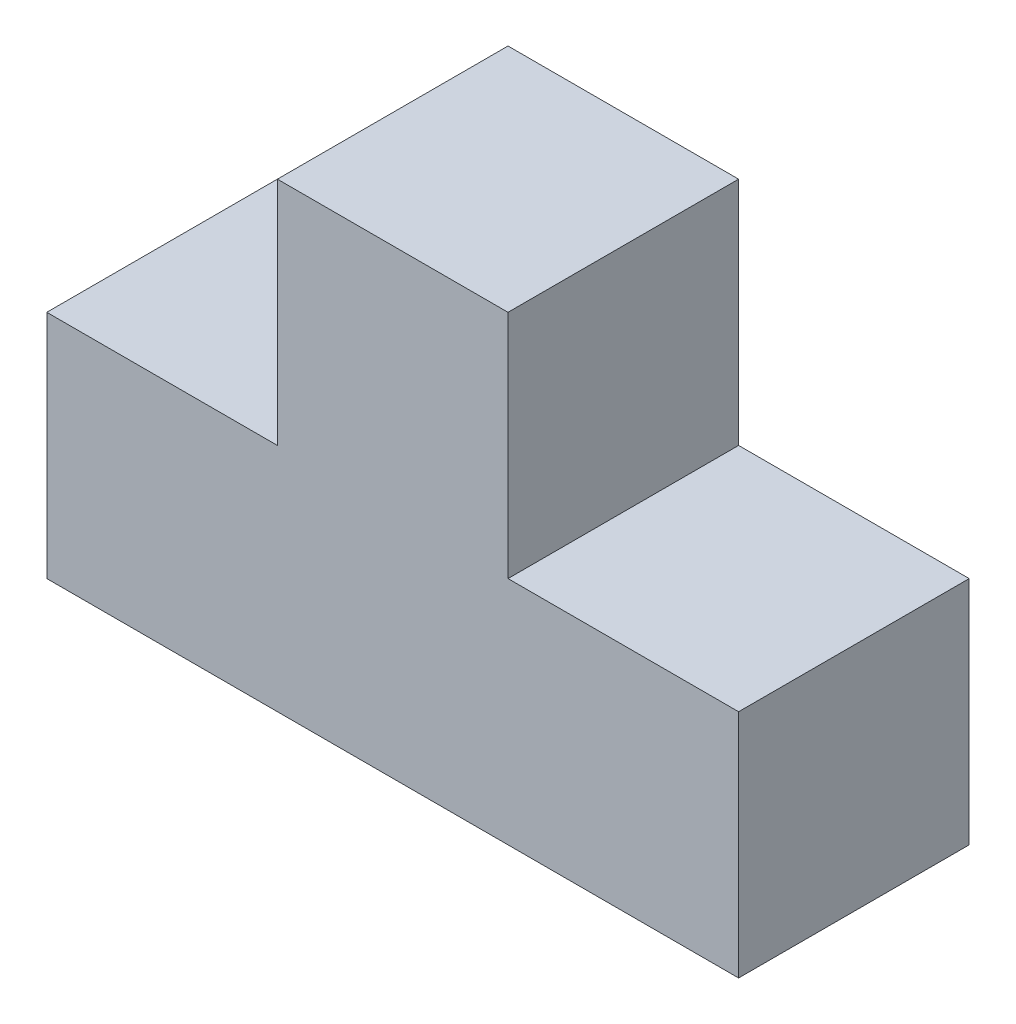
SolidWorks part; units mm, degrees
ref_plane "Front Plane" through (0, 0, 0) normal (0, 0, 1) x (1, 0, 0)
ref_plane "Top Plane" through (0, 0, 0) normal (0, 1, 0) x (1, 0, 0)
ref_plane "Right Plane" through (0, 0, 0) normal (1, 0, 0) x (0, 0, -1)
sketch "Sketch1" plane through (0, 0, 0) normal (0, 0, 1) x (1, 0, 0)
  line L0 (-50.7257, 17.8333) -> (-50.7257, 7.8333)
  line L1 (-50.7257, 17.8333) -> (-40.7257, 17.8333)
  line L2 (-40.7257, 17.8333) -> (-40.7257, 27.8333)
  line L3 (-40.7257, 27.8333) -> (-30.7257, 27.8333)
  line L4 (-30.7257, 27.8333) -> (-30.7257, 17.8333)
  line L5 (-30.7257, 17.8333) -> (-20.7257, 17.8333)
  line L6 (-20.7257, 17.8333) -> (-20.7257, 7.8333)
  line L7 (-20.7257, 7.8333) -> (-46.2738, 7.8333)
  line L8 (-50.7257, 7.8333) -> (-46.2738, 7.8333)
extrude "Boss-Extrude1" add sketch "Sketch1" along normal blind 10
